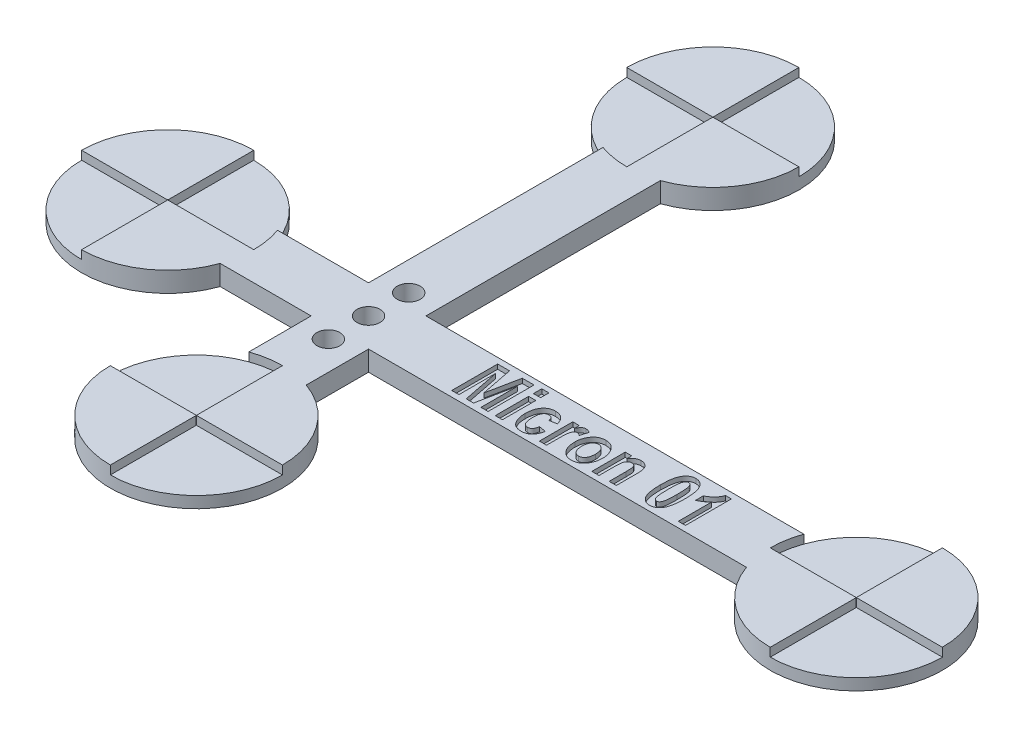
SolidWorks part; units mm, degrees
ref_plane "Front Plane" through (0, 0, 0) normal (0, 0, 1) x (1, 0, 0)
ref_plane "Top Plane" through (0, 0, 0) normal (0, 1, 0) x (1, 0, 0)
ref_plane "Right Plane" through (0, 0, 0) normal (1, 0, 0) x (0, 0, -1)
sketch "Sketch1" plane through (0, 0, 0) normal (0, 1, 0) x (1, 0, 0)
  line L0 (0, 0) -> (120, 0) construction
  line L1 (35, -30) -> (35, 60) construction
  line L2 (30, 45.8579) -> (30, 5)
  line L3 (40, -15.8579) -> (40, -5)
  line L4 (14.1421, 5) -> (30, 5)
  line L5 (105.8579, -5) -> (40, -5)
  line L6 (40, 5) -> (105.8579, 5)
  line L7 (30, -5) -> (30, -15.8579)
  line L8 (30, -5) -> (14.1421, -5)
  line L9 (40, 5) -> (40, 45.8579)
  arc A0 (14.1421, 5) -> (14.1421, -5) centre (0, 0) ccw
  arc A1 (105.8579, -5) -> (105.8579, 5) centre (120, 0) ccw
  arc A2 (40, 45.8579) -> (30, 45.8579) centre (35, 60) ccw
  arc A3 (30, -15.8579) -> (40, -15.8579) centre (35, -30) ccw
  dimension "D1" = 30
  dimension "D3" = 30
  dimension "D5" = 30
  dimension "D6" = 30
  dimension "D2" = 120
  dimension "D4" = 35
  dimension "D7" = 90
  dimension "D8" = 60
  dimension "D9" = 5
  dimension "D10" = 5
  dimension "D11" = 5
  dimension "D12" = 5
extrude "Boss-Extrude1" add sketch "Sketch1" along normal blind 3.5
sketch "Sketch2" plane through (0, 3.5, 0) normal (0, 1, 0) x (1, 0, 0)
  line L0 (-15, 0) -> (-0.05, 0)
  line L1 (35, 75) -> (35, 60.05)
  line L2 (20, 60) -> (34.95, 60)
  line L3 (120, 15) -> (120, 0.05)
  line L4 (0, 15) -> (0, 0.05)
  line L5 (20, -30) -> (34.95, -30)
  line L6 (35.05, 60) -> (50, 60)
  line L7 (35, 59.95) -> (35, 45)
  line L8 (35, -30.05) -> (35, -45)
  line L9 (35.05, -30) -> (50, -30)
  line L10 (0, -0.05) -> (0, -15)
  line L11 (0.05, 0) -> (15, 0)
  line L12 (120, -0.05) -> (120, -15)
  line L13 (120.05, 0) -> (135, 0)
  line L14 (105, 0) -> (119.95, 0)
  line L15 (35, -15) -> (35, -29.95)
  arc A0 (20, 60) -> (35, 45) centre (35, 60) ccw
  arc A1 (-15, 0) -> (0, -15) centre (0, 0) ccw
  arc A2 (35, -45) -> (50, -30) centre (35, -30) ccw
  arc A3 (120, 15) -> (105, 0) centre (120, 0) ccw
  arc A4 (0, 0.05) -> (-0.05, 0) centre (0, 0) ccw
  arc A5 (35, 59.95) -> (35.05, 60) centre (35, 60) ccw
  arc A6 (119.95, 0) -> (120, -0.05) centre (120, 0) ccw
  arc A7 (34.95, -30) -> (35, -30.05) centre (35, -30) ccw
  arc A8 (35, 60.05) -> (34.95, 60) centre (35, 60) ccw
  arc A9 (50, 60) -> (35, 75) centre (35, 60) ccw
  arc A10 (35.05, -30) -> (35, -29.95) centre (35, -30) ccw
  arc A11 (35, -15) -> (20, -30) centre (35, -30) ccw
  arc A12 (0, -0.05) -> (0.05, 0) centre (0, 0) ccw
  arc A13 (15, 0) -> (0, 15) centre (0, 0) ccw
  arc A14 (120.05, 0) -> (120, 0.05) centre (120, 0) ccw
  arc A15 (120, -15) -> (135, 0) centre (120, 0) ccw
  dimension "D1" = 0.1
  dimension "D2" = 0.1
  dimension "D3" = 0.1
  dimension "D4" = 0.1
extrude "Cut-Extrude1" cut sketch "Sketch2" against normal blind 1.5
sketch "Sketch3" plane through (0, 3.5, 0) normal (0, 1, 0) x (1, 0, 0)
  line L0 (50.4289, -4) -> (95.4289, -4) construction
  line L1 (40, -5) -> (105.8579, -5) construction
  text T0 "<b>Micron 01</b>" font "Arial Narrow" height 8
  point P4 (72.9289, -4)
  point P5 (72.9289, -5)
  dimension "D1" = 45
  dimension "D2" = 1
extrude "Cut-Extrude2" cut sketch "Sketch3" against normal blind 0.8
sketch "Sketch4" plane through (0, 3.5, 0) normal (0, 1, 0) x (1, 0, 0)
  line L0 (35, 7) -> (35, -7) construction
  line L1 (0.05, 0) -> (15, 0) construction
  line L2 (35, -29.95) -> (35, -15) construction
  circle A0 centre (35, 0) radius 2
  circle A1 centre (35, 7) radius 2
  circle A2 centre (35, -7) radius 2
  point P4 (35, 0)
  dimension "D1" = 4
  dimension "D3" = 4
  dimension "D4" = 4
  dimension "D2" = 14
extrude "Cut-Extrude3" cut sketch "Sketch4" against normal through all
